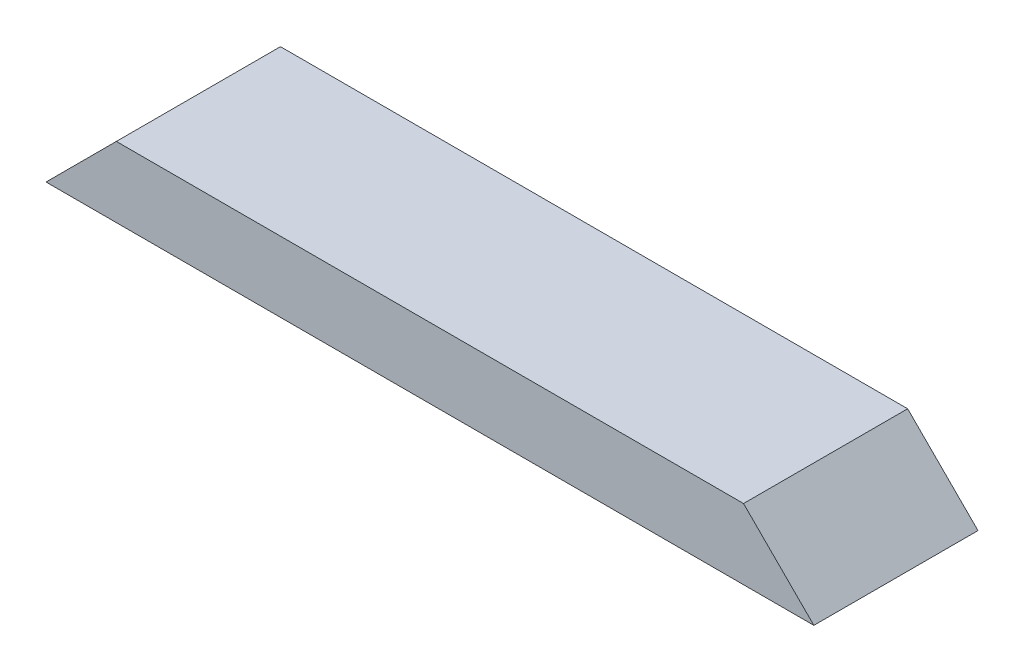
SolidWorks part; units mm, degrees
material "Pine"
ref_plane "Front Plane" through (0, 0, 0) normal (0, 0, 1) x (1, 0, 0)
ref_plane "Top Plane" through (0, 0, 0) normal (0, 1, 0) x (1, 0, 0)
ref_plane "Right Plane" through (0, 0, 0) normal (1, 0, 0) x (0, 0, -1)
sketch "Sketch1" plane through (0, 0, 0) normal (0, 1, 0) x (1, 0, 0)
  line L1 (0, 0) -> (415.925, 0)
  line L2 (0, 0) -> (0, 88.9)
  line L3 (0, 88.9) -> (415.925, 88.9)
  line L4 (415.925, 0) -> (415.925, 88.9)
  dimension "D1" = 88.9
  dimension "D2" = 415.925
extrude "Boss-Extrude1" add sketch "Sketch1" along normal blind 38.1
sketch "Sketch2" plane through (0, 0, 0) normal (0, 0, 1) x (1, 0, 0)
  line L0 (0, 0) -> (38.1, 38.1)
  line L1 (0, 38.1) -> (415.925, 38.1) construction
  line L2 (38.1, 38.1) -> (0, 38.1)
  line L3 (0, 38.1) -> (0, 0)
  line L5 (415.925, 0) -> (415.925, 38.1)
  line L9 (415.925, 38.1) -> (377.825, 38.1)
  line L10 (377.825, 38.1) -> (415.925, 0)
  dimension "D1" = 38.1
  dimension "D2" = 38.1
  dimension "D3" = 38.1
extrude "Cut-Extrude1" cut sketch "Sketch2" against normal through all
